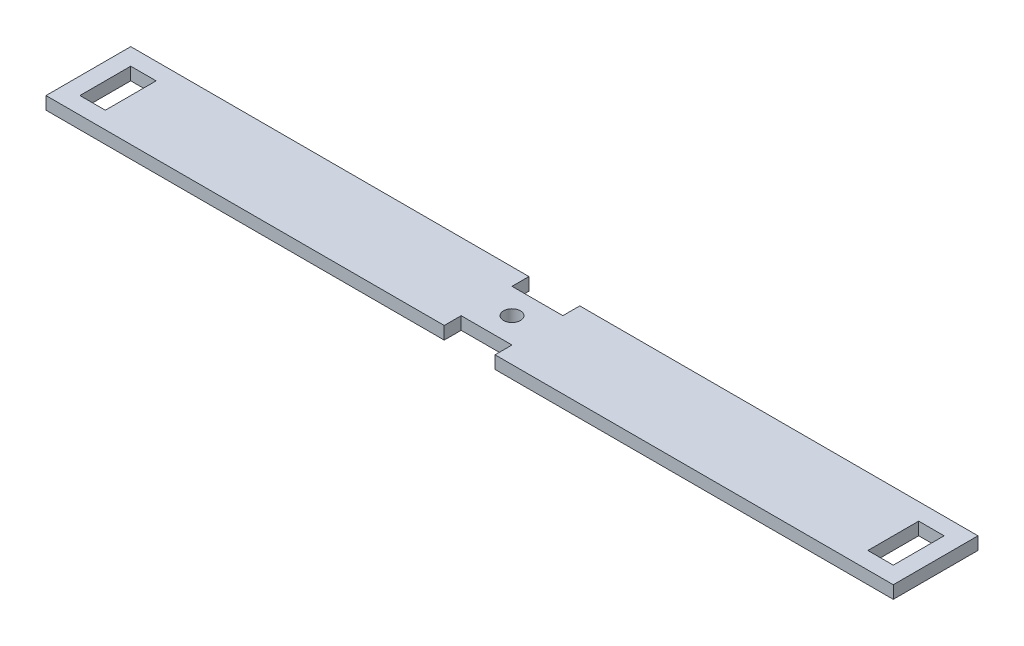
SolidWorks part; units mm, degrees
ref_plane "Front Plane" through (0, 0, 0) normal (0, 0, 1) x (1, 0, 0)
ref_plane "Top Plane" through (0, 0, 0) normal (0, 1, 0) x (1, 0, 0)
ref_plane "Right Plane" through (0, 0, 0) normal (1, 0, 0) x (0, 0, -1)
sketch "Sketch1" plane through (0, 0, 0) normal (0, 1, 0) x (1, 0, 0)
  line L1 (-9.8298, 5.8807) -> (90.1702, 5.8807)
  line L2 (-9.8298, 5.8807) -> (-9.8298, -4.1193)
  line L3 (-9.8298, -4.1193) -> (90.1702, -4.1193)
  line L4 (90.1702, 5.8807) -> (90.1702, -4.1193)
  dimension "D1" = 10
  dimension "D2" = 100
extrude "Boss-Extrude1" add sketch "Sketch1" along normal blind 1.5
sketch "Sketch2" plane through (0, 1.5, 0) normal (0, 1, 0) x (1, 0, 0)
  line L4 (90.1702, 5.8807) -> (-9.8298, 5.8807) construction
  line L5 (40.1702, 5.8807) -> (40.1702, -4.1193) construction
  line L6 (-9.8298, 0.8807) -> (90.1702, 0.8807) construction
  line L7 (-9.8298, 5.8807) -> (-9.8298, -4.1193) construction
  line L8 (90.1702, -4.1193) -> (90.1702, 5.8807) construction
  circle A0 centre (40.1702, 0.8807) radius 1
  dimension "D1" = 2
extrude "Cut-Extrude2" cut sketch "Sketch2" against normal blind 2 contours A0
sketch "Sketch5" plane through (0, 1.5, 0) normal (0, 1, 0) x (1, 0, 0)
  line L0 (90.1702, 5.8807) -> (-9.8298, 5.8807) construction
  line L5 (-9.8298, -4.1193) -> (90.1702, -4.1193) construction
  line L6 (37.1702, 5.8807) -> (43.1702, 5.8807)
  line L7 (37.1702, 5.8807) -> (37.1702, 3.8807)
  line L8 (37.1702, 3.8807) -> (43.1702, 3.8807)
  line L9 (43.1702, 5.8807) -> (43.1702, 3.8807)
  line L19 (37.1702, -4.1193) -> (43.1702, -4.1193)
  line L20 (37.1702, -4.1193) -> (37.1702, -2.1193)
  line L21 (37.1702, -2.1193) -> (43.1702, -2.1193)
  line L22 (43.1702, -4.1193) -> (43.1702, -2.1193)
  line L28 (40.1702, -4.1193) -> (40.1702, 5.8807) construction
  line L29 (-9.8298, 5.8807) -> (-9.8298, -4.1193) construction
  line L30 (-7.8298, 3.8807) -> (-4.8298, 3.8807)
  line L31 (-7.8298, 3.8807) -> (-7.8298, -2.1193)
  line L32 (-7.8298, -2.1193) -> (-4.8298, -2.1193)
  line L33 (-4.8298, 3.8807) -> (-4.8298, -2.1193)
  line L34 (90.1702, -4.1193) -> (90.1702, 5.8807) construction
  line L35 (88.1702, 3.8807) -> (85.1702, 3.8807)
  line L36 (88.1702, 3.8807) -> (88.1702, -2.1193)
  line L37 (88.1702, -2.1193) -> (85.1702, -2.1193)
  line L38 (85.1702, 3.8807) -> (85.1702, -2.1193)
  dimension "D1" = 2
  dimension "D2" = 3
  dimension "D3" = 2
  dimension "D4" = 6
  dimension "D5" = 3
  dimension "D6" = 6
  dimension "D7" = 2
extrude "Cut-Extrude4" cut sketch "Sketch5" against normal blind 2
